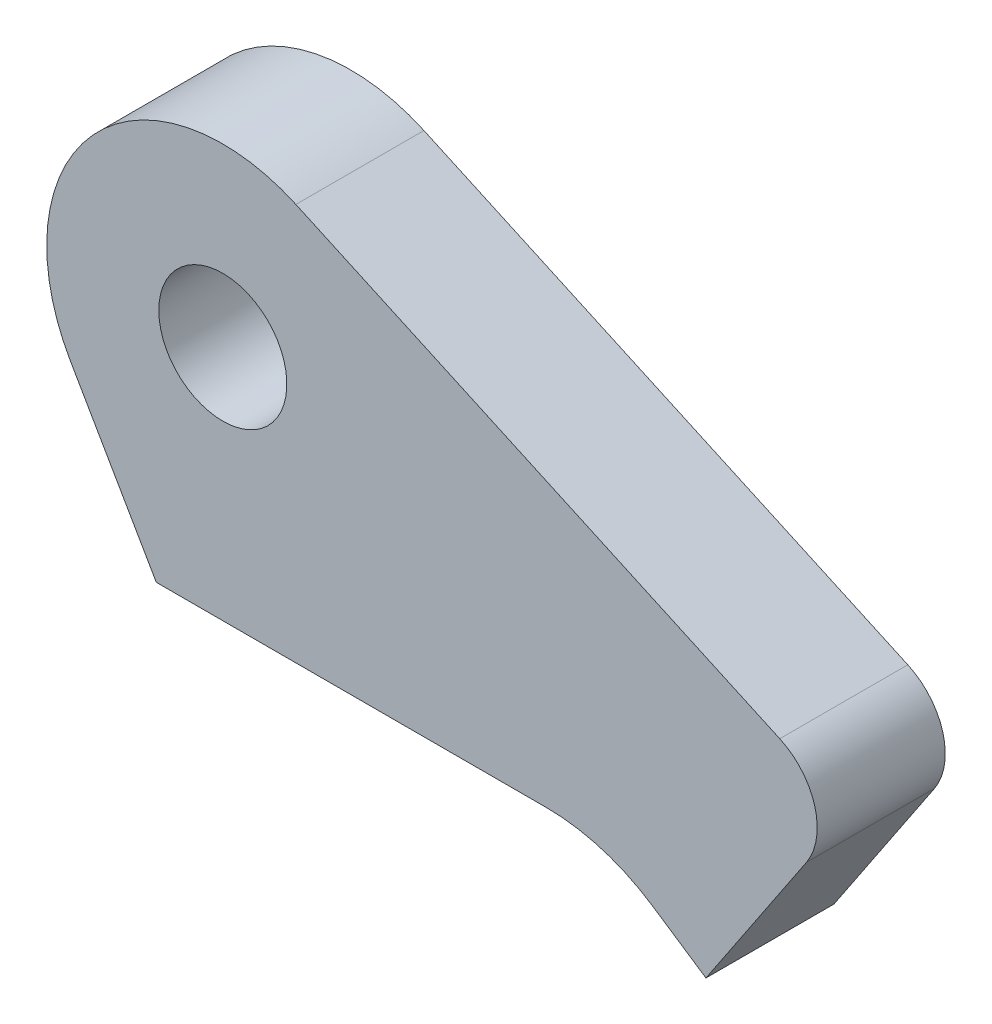
SolidWorks part; units mm, degrees
material "2024 Alloy"
ref_plane "Plane1" through (0, 0, 0) normal (0, 0, 1) x (1, 0, 0)
ref_plane "Plane2" through (0, 0, 0) normal (0, 1, 0) x (1, 0, 0)
ref_plane "Plane3" through (0, 0, 0) normal (1, 0, 0) x (0, 0, -1)
sketch "Sketch1" plane through (0, 0, 0) normal (0, 0, 1) x (1, 0, 0)
  line L0 (17.1452, 27.7178) -> (28.26, 44.345)
  line L1 (28.027, 20.4436) -> (13.0025, 30.4871) construction
  line L2 (-25.7817, 33.0167) -> (-32.4934, 44.6417)
  line L3 (4.6664, 33.0167) -> (-25.1296, 33.0167) construction
  line L4 (4.6664, 33.0167) -> (-25.7817, 33.0167)
  line L5 (17.1452, 27.7178) -> (13.0025, 30.4871)
  line L6 (28.26, 44.345) -> (-14.8782, 64.0263)
  arc A0 (13.0025, 30.4871) -> (4.6664, 33.0167) centre (4.6664, 18.0167) ccw construction
  arc A1 (13.0025, 30.4871) -> (4.6664, 33.0167) centre (4.6664, 18.0167) ccw
  arc A2 (-14.8782, 64.0263) -> (-32.4934, 44.6417) centre (-20.5856, 51.5167) ccw
  dimension "D3" = 13.75
  dimension "D1" = 20
  dimension "D2" = 42.927
  dimension "D4" = 120
  dimension "D5" = 18.5
extrude "Base-Extrude" add sketch "Sketch1" against normal blind 10
sketch "Sketch2" plane through (0, 0, -10) normal (0, 0, -1) x (-1, 0, 0)
  circle A0 centre (20.5856, 51.5167) radius 5
  arc A1 (32.4934, 44.6417) -> (14.8782, 64.0263) centre (20.5856, 51.5167) ccw construction
  dimension "D1" = 10
extrude "Cut-Extrude1" cut sketch "Sketch2" against normal through all
fillet "Fillet1" radius 5 1 edges at (28.26, 44.345, -5)
